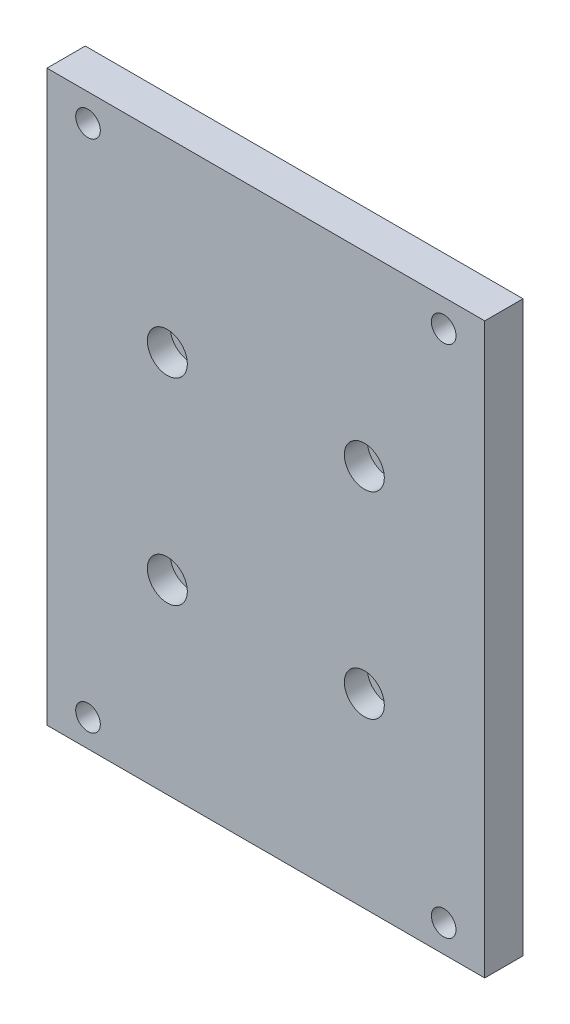
SolidWorks part; units mm, degrees
ref_plane "前基準面" through (0, 0, 0) normal (0, 0, 1) x (1, 0, 0)
ref_plane "上基準面" through (0, 0, 0) normal (0, 1, 0) x (1, 0, 0)
ref_plane "右基準面" through (0, 0, 0) normal (1, 0, 0) x (0, 0, -1)
sketch "草圖2" plane through (0, 0, 0) normal (0, 0, 1) x (1, 0, 0)
  line L0 (0, 0) -> (0, 30.0174) construction
  line L1 (-40, 52) -> (40, 52)
  line L2 (-40, 52) -> (-40, -52)
  line L3 (-40, -52) -> (40, -52)
  line L4 (40, 52) -> (40, -52)
  line L5 (-40, 52) -> (40, -52) construction
  line L6 (-40, -52) -> (40, 52) construction
  line L7 (0, -3.85) -> (0, 3.85) construction
  line L8 (0, 0) -> (-44.8344, 0) construction
  line L9 (3.85, 0) -> (-3.85, 0) construction
  line L10 (57, 0) -> (12.1656, 0) construction
  line L11 (57, -36) -> (12.1656, -36) construction
  line L12 (0, -36) -> (-44.8344, -36) construction
  circle A0 centre (-18, 18) radius 2.25
  circle A1 centre (-32.5, 47) radius 2.25
  circle A2 centre (18, 18) radius 2.25
  circle A3 centre (18, -18) radius 2.25
  circle A4 centre (-18, -18) radius 2.25
  circle A8 centre (32.5, 47) radius 2.25
  circle A9 centre (32.5, -47) radius 2.25
  circle A10 centre (-32.5, -47) radius 2.25
  point P0 (0, 0)
  dimension "D3" = 4.5
  dimension "D6" = 4.5
  dimension "D9" = 32.5
  dimension "D10" = 47
  dimension "D1" = 80
  dimension "D2" = 104
  dimension "D4" = 36
  dimension "D5" = 36
extrude "填料-伸長1" add sketch "草圖2" along normal blind 7
hole_wizard "鑽孔1" positions "3D草圖1" profile "草圖3" legacy end condition through all
sketch3d "3D草圖1"
  line L0 (-18, 18, 7) -> (-18, 18, 0) construction
  line L1 (18, 18, 7) -> (18, 18, 0) construction
  line L2 (18, -18, 7) -> (18, -18, 0) construction
  line L3 (-18, -18, 7) -> (-18, -18, 0) construction
  point P0 (-18, 18, 7)
  point P4 (18, 18, 7)
  point P8 (18, -18, 7)
  point P12 (-18, -18, 7)
sketch "草圖3" plane through (-18, 18, 7) normal (1, 0, 0) x (0, -1, 0)
  line L0 (0, 0) -> (0, 7)
  line L1 (0, 7) -> (2.25, 7)
  line L2 (2.25, 7) -> (2.25, 4.2)
  line L3 (2.25, 4.2) -> (3.65, 4.2)
  line L4 (3.65, 4.2) -> (3.65, 0)
  line L5 (3.65, 0) -> (0, 0)
  line L6 (0, 110) -> (0, -10) construction
  dimension "直徑" = 4.5
  dimension "深度" = 7
  dimension "柱孔直徑1" = 7.3
  dimension "柱孔深度1" = 4.2
sketch "草圖4" plane through (0, 0, 0) normal (0, 0, -1) x (-1, 0, 0)
  line L0 (0, 3.85) -> (0, -3.85) construction
  line L1 (-28.2853, 47) -> (-30.3927, 50.65)
  line L2 (-30.3927, 50.65) -> (-34.6073, 50.65)
  line L3 (-34.6073, 50.65) -> (-36.7147, 47)
  line L4 (-36.7147, 47) -> (-34.6073, 43.35)
  line L5 (-34.6073, 43.35) -> (-30.3927, 43.35)
  line L6 (-30.3927, 43.35) -> (-28.2853, 47)
  line L25 (30.3927, 43.35) -> (28.2853, 47)
  line L26 (34.6073, 43.35) -> (30.3927, 43.35)
  line L27 (36.7147, 47) -> (34.6073, 43.35)
  line L28 (34.6073, 50.65) -> (36.7147, 47)
  line L29 (30.3927, 50.65) -> (34.6073, 50.65)
  line L30 (28.2853, 47) -> (30.3927, 50.65)
  line L31 (3.85, 0) -> (-3.85, 0) construction
  line L32 (28.2853, -47) -> (30.3927, -50.65)
  line L33 (30.3927, -50.65) -> (34.6073, -50.65)
  line L34 (34.6073, -50.65) -> (36.7147, -47)
  line L35 (36.7147, -47) -> (34.6073, -43.35)
  line L36 (34.6073, -43.35) -> (30.3927, -43.35)
  line L37 (30.3927, -43.35) -> (28.2853, -47)
  line L38 (-30.3927, -43.35) -> (-28.2853, -47)
  line L39 (-34.6073, -43.35) -> (-30.3927, -43.35)
  line L40 (-36.7147, -47) -> (-34.6073, -43.35)
  line L41 (-34.6073, -50.65) -> (-36.7147, -47)
  line L42 (-30.3927, -50.65) -> (-34.6073, -50.65)
  line L43 (-28.2853, -47) -> (-30.3927, -50.65)
  circle A0 centre (-32.5, 47) radius 3.65 construction
  circle A1 centre (32.5, 47) radius 3.65 construction
  circle A2 centre (32.5, -47) radius 3.65 construction
  circle A3 centre (-32.5, -47) radius 3.65 construction
  dimension "D1" = 7.3
extrude "除料-伸長1" cut sketch "草圖4" against normal blind 2.5
